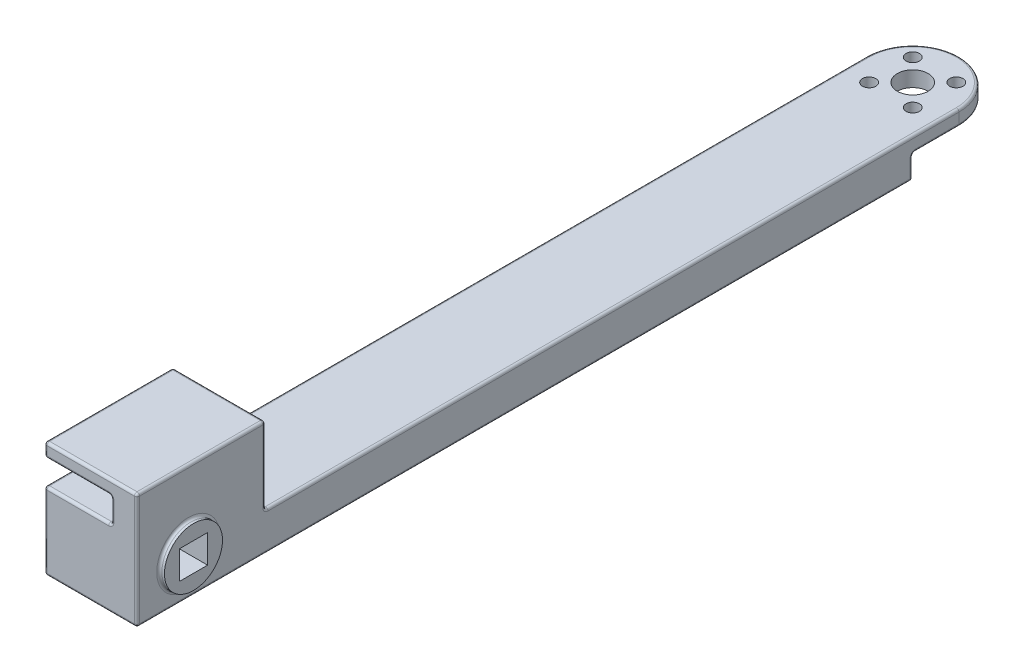
SolidWorks part; units mm, degrees
ref_plane "Front Plane" through (0, 0, 0) normal (0, 0, 1) x (1, 0, 0)
ref_plane "Top Plane" through (0, 0, 0) normal (0, 1, 0) x (1, 0, 0)
ref_plane "Right Plane" through (0, 0, 0) normal (1, 0, 0) x (0, 0, -1)
sketch "Sketch1" plane through (0, 0, 0) normal (0, 0, 1) x (1, 0, 0)
  line L1 (0, 0) -> (18, 0)
  line L2 (0, 0) -> (0, 15)
  line L3 (0, 15) -> (18, 15)
  line L4 (18, 0) -> (18, 15)
  dimension "D1" = 18
  dimension "D2" = 15
extrude "Boss-Extrude1" add sketch "Sketch1" along normal blind 40 and the other way blind 150
sketch "Sketch2" plane through (18, 0, 0) normal (1, 0, 0) x (0, 0, -1)
  line L0 (0, 0) -> (0, 15) construction
  line L1 (150, 15) -> (-40, 15) construction
  circle A0 centre (0, 7.5) radius 5.65
  dimension "D1" = 11.3
extrude "Boss-Extrude2" add sketch "Sketch2" along normal blind 1 contours A0
ref_plane "Plane1" through (9, 0, 0) normal (1, 0, 0) x (0, 0, -1)
mirror "Mirror1" about plane through (9, 0, 0) normal (1, 0, 0) of "Boss-Extrude2"
sketch "Sketch3" plane through (19, 0, 0) normal (1, 0, 0) x (0, 0, -1)
  line L1 (-2.75, 4.75) -> (2.75, 4.75)
  line L2 (-2.75, 4.75) -> (-2.75, 10.25)
  line L3 (-2.75, 10.25) -> (2.75, 10.25)
  line L4 (2.75, 4.75) -> (2.75, 10.25)
  line L5 (-2.75, 4.75) -> (2.75, 10.25) construction
  line L6 (-2.75, 10.25) -> (2.75, 4.75) construction
  point P0 (0, 7.5)
  dimension "D1" = 5.5
  dimension "D2" = 5.5
extrude "Cut-Extrude1" cut sketch "Sketch3" against normal up to next
sketch "Sketch4" plane through (18, 0, 0) normal (1, 0, 0) x (0, 0, -1)
  line L1 (150, 15) -> (15, 15)
  line L2 (150, 15) -> (150, 7.5)
  line L3 (150, 7.5) -> (15, 7.5)
  line L4 (15, 15) -> (15, 7.5)
  line L5 (-40, 15) -> (-10, 15)
  line L6 (-40, 15) -> (-40, 0)
  line L7 (-40, 0) -> (-10, 0)
  line L8 (-10, 15) -> (-10, 0)
  dimension "D1" = 135
  dimension "D2" = 7.5
  dimension "D3" = 30
  dimension "D4" = 15
extrude "Cut-Extrude2" cut sketch "Sketch4" against normal up to next
sketch "Sketch6" plane through (0, 7.5, 0) normal (0, 1, 0) x (1, 0, 0)
  line L0 (0, 150) -> (18, 150) construction
  circle A0 centre (9, 150) radius 9
extrude "Boss-Extrude4" add sketch "Sketch6" against normal blind 3
sketch "Sketch9" plane through (0, 4.5, 0) normal (0, -1, 0) x (-1, 0, 0)
  line L0 (-9, 150) -> (-9, 156) construction
  line L1 (-9, 150) -> (-4.7574, 154.2426) construction
  line L2 (0, 150) -> (-18, 150) construction
  circle A0 centre (-9, 150) radius 3
  circle A1 centre (-4.7574, 154.2426) radius 1.3
  circle A5 centre (-9, 150) radius 9 construction
  circle A6 centre (-4.7574, 145.7574) radius 1.3
  circle A7 centre (-13.2426, 145.7574) radius 1.3
  circle A8 centre (-13.2426, 154.2426) radius 1.3
  point P19 (-9, 150)
  dimension "D1" = 6
  dimension "D5" = 2.6
  dimension "D2" = 6
  dimension "D3" = 45
  dimension "D4" = 6
  dimension "D6" = 4
extrude "Cut-Extrude3" cut sketch "Sketch9" against normal blind 3
sketch "Sketch16" plane through (18, 0, 0) normal (1, 0, 0) x (0, 0, -1)
  line L0 (150, 0) -> (-10, 0) construction
  line L1 (150, 4.5) -> (141, 4.5)
  line L2 (150, 4.5) -> (150, 0)
  line L3 (150, 0) -> (141, 0)
  line L4 (141, 4.5) -> (141, 0)
  dimension "D1" = 9
extrude "Cut-Extrude5" cut sketch "Sketch16" against normal up to next
sketch "Sketch15" plane through (0, 0, 10) normal (0, 0, 1) x (1, 0, 0)
  line L0 (18, 15) -> (13, 15)
  line L1 (0, 15) -> (18, 15) construction
  line L2 (13, 15) -> (13, 19.8)
  line L3 (18, 15) -> (18, 22.5)
  line L4 (18, 22.5) -> (0, 22.5)
  line L5 (0, 22.5) -> (0, 19.8)
  line L6 (0, 19.8) -> (13, 19.8)
  dimension "D1" = 5
  dimension "D2" = 4.8
  dimension "D3" = 7.5
extrude "Boss-Extrude7" add sketch "Sketch15" against normal blind 25
fillet "Fillet2" radius 0.5 36 edges at (9, 4.5, -159) (9, 7.5, -159) (9, 4.5, -141) (9, 0, -141) (0, 1.85, 0) (0, 0, -65.5) (0, 2.25, -141) (0, 4.5, -145.5) (18, 13.15, 0) (18, 2.25, -141) (18, 0, -65.5) (18, 4.5, -145.5) (0, 7.5, -82.5) (18, 7.5, -82.5) (0, 11.25, -15) (9, 7.5, -15) (18, 15, -15) (6.5, 19.8, 10) (6.5, 19.8, -15) (0, 19.8, -2.5) (0, 21.15, 10) (0, 21.15, -15) (13, 17.4, 10) (13, 17.4, -15) (13, 19.8, -2.5) (0, 15, -2.5) (6.5, 15, -15) (13, 15, -2.5) (0, 7.5, 10) (6.5, 15, 10) (18, 11.25, 10) (9, 0, 10) (0, 22.5, -2.5) (9, 22.5, 10) (9, 22.5, -15) (18, 22.5, -2.5)
